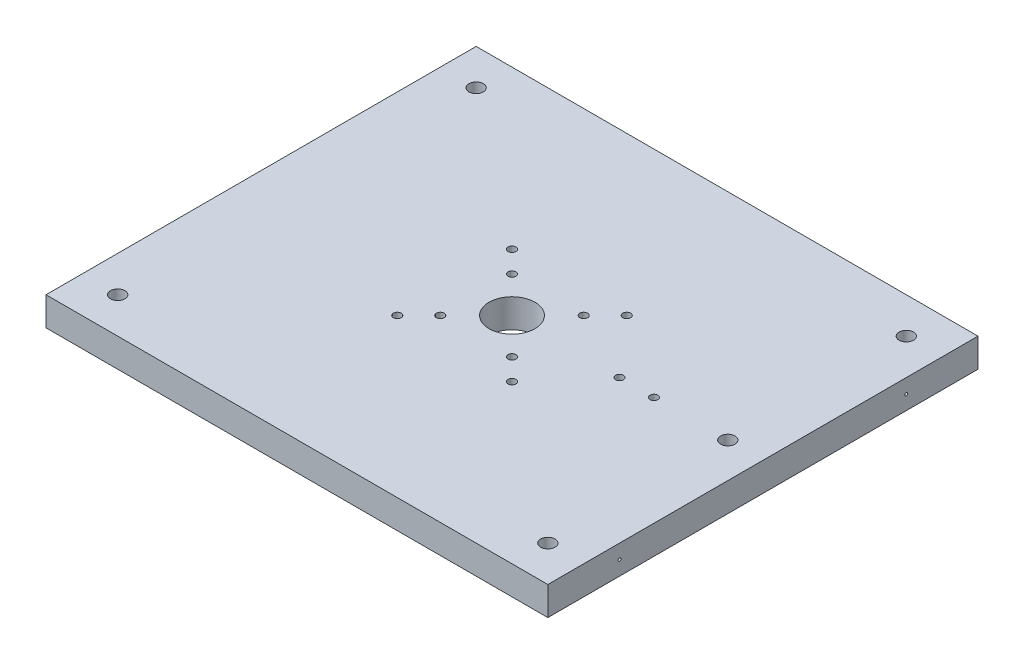
SolidWorks part; units mm, degrees
ref_plane "Front Plane" through (0, 0, 0) normal (0, 0, 1) x (1, 0, 0)
ref_plane "Top Plane" through (0, 0, 0) normal (0, 1, 0) x (1, 0, 0)
ref_plane "Right Plane" through (0, 0, 0) normal (1, 0, 0) x (0, 0, -1)
sketch "Sketch1" plane through (0, 0, 0) normal (0, 1, 0) x (1, 0, 0)
  line L1 (175, 150) -> (-175, 150)
  line L2 (175, 150) -> (175, -150)
  line L3 (175, -150) -> (-175, -150)
  line L4 (-175, 150) -> (-175, -150)
  line L5 (175, 150) -> (-175, -150) construction
  line L6 (175, -150) -> (-175, 150) construction
  point P0 (0, 0)
  dimension "D1" = 350
  dimension "D2" = 300
extrude "Boss-Extrude1" add sketch "Sketch1" along normal blind 20
sketch "Sketch2" plane through (0, 20, 0) normal (0, 1, 0) x (1, 0, 0)
  line L0 (-175, -150) -> (175, -150) construction
  line L1 (-175, 150) -> (-175, -150) construction
  circle A0 centre (-150, -125) radius 5
  circle A1 centre (-150, 125) radius 5
  circle A2 centre (150, 125) radius 5
  circle A3 centre (150, -125) radius 5
  dimension "D1" = 10
  dimension "D2" = 25
  dimension "D3" = 25
  dimension "D4" = 2
  dimension "D5" = 2
extrude "Cut-Extrude1" cut sketch "Sketch2" against normal through all
sketch "Sketch3" plane through (0, 20, 0) normal (0, 1, 0) x (1, 0, 0)
  line L0 (175, -150) -> (175, 150) construction
  line L1 (175, 150) -> (-175, 150) construction
  circle A0 centre (75, 0) radius 2.75
  circle A1 centre (99, 0) radius 2.75
  dimension "D1" = 5.5
  dimension "D2" = 5.5
  dimension "D3" = 76
  dimension "D4" = 24
  dimension "D5" = 150
  dimension "D6" = 150
extrude "Cut-Extrude2" cut sketch "Sketch3" against normal blind 20
sketch "Sketch4" plane through (0, 20, 0) normal (0, 1, 0) x (1, 0, 0)
  line L0 (175, -150) -> (175, 150) construction
  circle A0 centre (150.5, 0) radius 5
  dimension "D1" = 24.5
  dimension "D2" = 10
extrude "Cut-Extrude3" cut sketch "Sketch4" against normal blind 20
sketch "Sketch5" plane through (0, 20, 0) normal (0, 1, 0) x (1, 0, 0)
  line L0 (0, 0) -> (-40, 40) construction
  line L1 (-40, 40) -> (-40, 0) construction
  line L2 (-40, 0) -> (0, 0) construction
  circle A0 centre (-40, 40) radius 2.75
  circle A1 centre (40, 40) radius 2.75
  circle A2 centre (40, -40) radius 2.75
  circle A3 centre (-40, -40) radius 2.75
  dimension "D1" = 5.5
  dimension "D2" = 40
  dimension "D3" = 40
  dimension "D4" = 2
  dimension "D5" = 2
extrude "Cut-Extrude4" cut sketch "Sketch5" against normal blind 20
sketch "Sketch6" plane through (0, 20, 0) normal (0, 1, 0) x (1, 0, 0)
  circle A0 centre (0, 0) radius 16
  dimension "D1" = 32
extrude "Cut-Extrude5" cut sketch "Sketch6" against normal blind 20
sketch "Sketch7" plane through (0, 20, 0) normal (0, 1, 0) x (1, 0, 0)
  line L0 (0, 0) -> (-25, 0) construction
  line L1 (-25, 0) -> (-25, 25) construction
  line L2 (-25, 25) -> (0, 0) construction
  circle A0 centre (-25, 25) radius 2.75
  circle A1 centre (25, 25) radius 2.75
  circle A2 centre (25, -25) radius 2.75
  circle A3 centre (-25, -25) radius 2.75
  dimension "D3" = 5.5
  dimension "D1" = 25
  dimension "D2" = 25
  dimension "D4" = 2
  dimension "D5" = 2
extrude "Cut-Extrude6" cut sketch "Sketch7" against normal blind 20
sketch "Sketch8" plane through (175, 0, 0) normal (1, 0, 0) x (0, 0, -1)
  line L0 (-150, 20) -> (-150, 0) construction
  line L1 (150, 20) -> (150, 0) construction
  circle A0 centre (-100, 10) radius 1
  circle A1 centre (100, 10) radius 1
  dimension "D1" = 2
  dimension "D2" = 2
  dimension "D3" = 50
  dimension "D4" = 50
extrude "Cut-Extrude7" cut sketch "Sketch8" against normal blind 15
